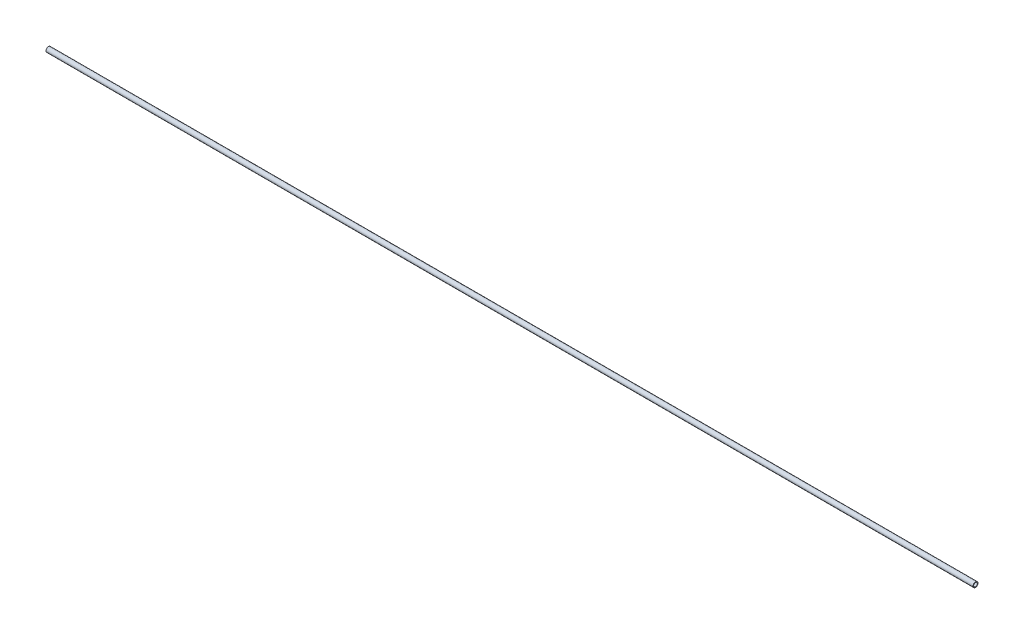
SolidWorks part; units mm, degrees
ref_plane "Alzado" through (0, 0, 0) normal (0, 0, 1) x (1, 0, 0)
ref_plane "Planta" through (0, 0, 0) normal (0, 1, 0) x (1, 0, 0)
ref_plane "Vista lateral" through (0, 0, 0) normal (1, 0, 0) x (0, 0, -1)
sketch "Croquis1" plane through (0, 0, 0) normal (1, 0, 0) x (0, 0, -1)
  circle A0 centre (0, 0) radius 6.35
  circle A1 centre (0, 0) radius 8.35
  dimension "D1" = 12.7
  dimension "D2" = 2
extrude "Saliente-Extruir1" add sketch "Croquis1" along normal mid plane 3140
